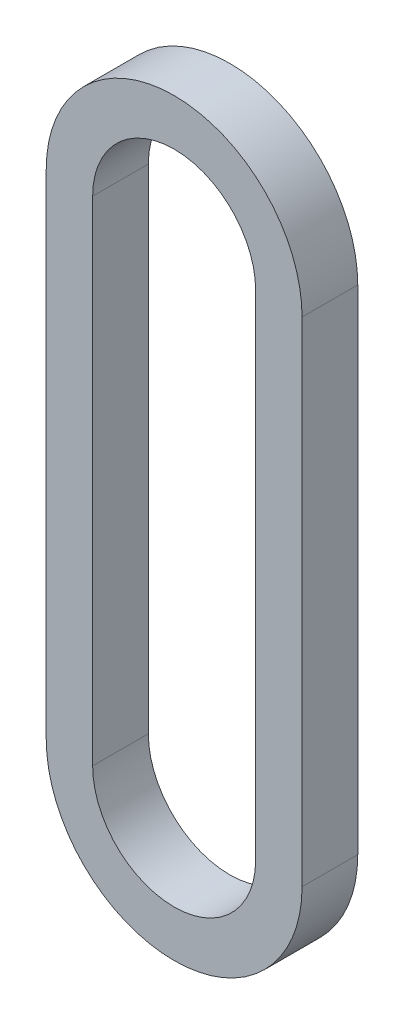
SolidWorks part; units mm, degrees
ref_plane "Front Plane" through (0, 0, 0) normal (0, 0, 1) x (1, 0, 0)
ref_plane "Top Plane" through (0, 0, 0) normal (0, 1, 0) x (1, 0, 0)
ref_plane "Right Plane" through (0, 0, 0) normal (1, 0, 0) x (0, 0, -1)
sketch "Sketch1" plane through (0, 0, 0) normal (0, 0, 1) x (1, 0, 0)
  line L0 (0, 0) -> (0, 67.5) construction
  line L1 (-11.1506, 0) -> (-11.1506, 67.5)
  line L2 (11.1506, 0) -> (11.1506, 67.5)
  line L3 (-17.5006, 0) -> (-17.5006, 67.5)
  line L4 (17.5006, 0) -> (17.5006, 67.5)
  arc A0 (-11.1506, 0) -> (11.1506, 0) centre (0, 0) ccw
  arc A1 (11.1506, 67.5) -> (-11.1506, 67.5) centre (0, 67.5) ccw
  arc A2 (17.5006, 67.5) -> (-17.5006, 67.5) centre (0, 67.5) ccw
  arc A3 (-17.5006, 0) -> (17.5006, 0) centre (0, 0) ccw
  point P3 (0, 33.75)
  dimension "D2" = 11.1506
  dimension "D1" = 67.5
  dimension "D3" = 6.35
extrude "Boss-Extrude1" add sketch "Sketch1" along normal blind 7.62
